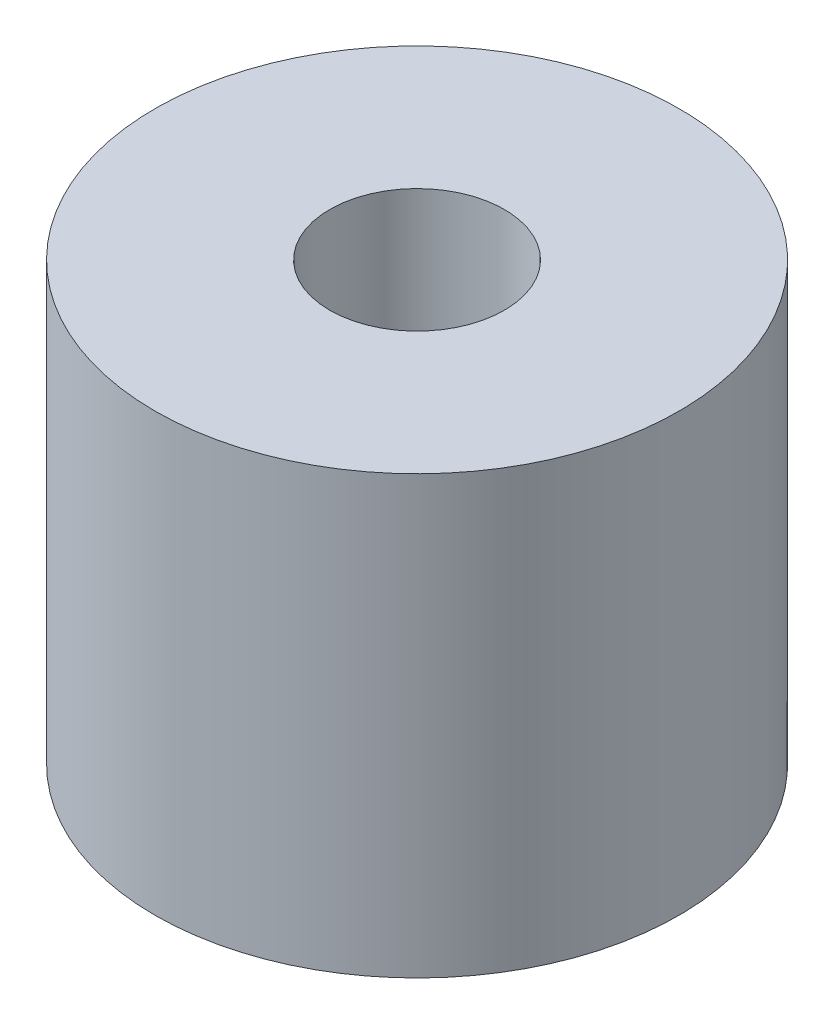
SolidWorks part; units mm, degrees
ref_plane "Front Plane" through (0, 0, 0) normal (0, 0, 1) x (1, 0, 0)
ref_plane "Top Plane" through (0, 0, 0) normal (0, 1, 0) x (1, 0, 0)
ref_plane "Right Plane" through (0, 0, 0) normal (1, 0, 0) x (0, 0, -1)
sketch "Sketch3" plane through (0, 0, 0) normal (0, 1, 0) x (1, 0, 0)
  circle A3 centre (0, 0) radius 2
  circle A4 centre (0, 0) radius 6
  dimension "D1" = 4
  dimension "D2" = 12
extrude "Boss-Extrude2" add sketch "Sketch3" along normal blind 10
